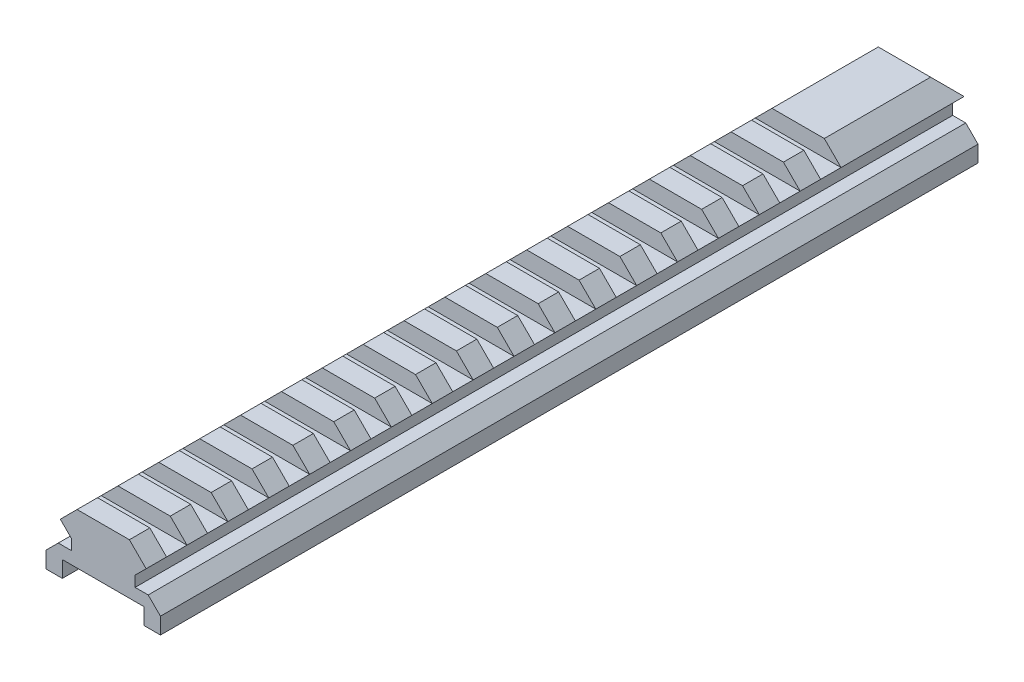
SolidWorks part; units mm, degrees
ref_plane "Front Plane" through (0, 0, 0) normal (0, 0, 1) x (1, 0, 0)
ref_plane "Top Plane" through (0, 0, 0) normal (0, 1, 0) x (1, 0, 0)
ref_plane "Right Plane" through (0, 0, 0) normal (1, 0, 0) x (0, 0, -1)
sketch "Sketch1" plane through (0, 0, 0) normal (0, 0, 1) x (1, 0, 0)
  line L0 (-14, 2.3) -> (-7.8, 2.3)
  line L1 (10, -4.7) -> (14, -4.7)
  line L2 (-14, 2.3) -> (-14, -4.7)
  line L3 (7.8, 2.3) -> (14, 2.3)
  line L4 (14, 2.3) -> (14, -4.7)
  line L5 (7.8, 4.9) -> (10.5, 7.6)
  line L6 (-14, -4.7) -> (-10, -4.7)
  line L7 (-6.4, 11.7) -> (6.4, 11.7)
  line L8 (-10, -4.7) -> (-10, -0.7)
  line L9 (-10.5, 7.6) -> (-7.8, 4.9)
  line L11 (6.4, 11.7) -> (10.5, 7.6)
  line L12 (-10.5, 7.6) -> (-6.4, 11.7)
  line L13 (-7.8, 2.3) -> (-7.8, 4.9)
  line L14 (7.8, 2.3) -> (7.8, 4.9)
  line L15 (10, -4.7) -> (10, -0.7)
  line L16 (-10, -0.7) -> (10, -0.7)
  dimension "D1" = 15.6
  dimension "D2" = 4
extrude "Boss-Extrude1" add sketch "Sketch1" along normal blind 200
chamfer "Chamfer1" distance 3 angle 45 2 edges at (14, 2.3, 100) (-14, 2.3, 100)
sketch "Sketch2" plane through (0, 0, 0) normal (1, 0, 0) x (0, 0, -1)
  line L0 (-195, 11.7) -> (-190, 11.7)
  line L1 (-200, 11.7) -> (0, 11.7) construction
  line L2 (-195, 11.7) -> (-195, 7.6)
  line L3 (-200, 7.6) -> (0, 7.6) construction
  line L4 (-195, 7.6) -> (-190, 7.6)
  line L5 (-190, 7.6) -> (-190, 11.7)
extrude "Cut-Extrude1" cut sketch "Sketch2" against normal blind 200 and the other way blind 200
pattern_linear "LPattern1" count 20 spacing 10 along (0, 0, -1) of "Cut-Extrude1"
sketch "Sketch4" plane through (0, 0, 25) normal (0, 0, -1) x (-1, 0, 0)
  line L0 (-10.5, 7.6) -> (10.5, 7.6)
  line L1 (10.5, 7.6) -> (6.4, 11.7)
  line L2 (6.4, 11.7) -> (-6.4, 11.7)
  line L3 (-6.4, 11.7) -> (-10.5, 7.6)
extrude "Boss-Extrude2" add sketch "Sketch4" along normal up to vertex (25 mm away)
chamfer "Chamfer2" distance 4 angle 45 1 edges at (0, 11.7, 0)
